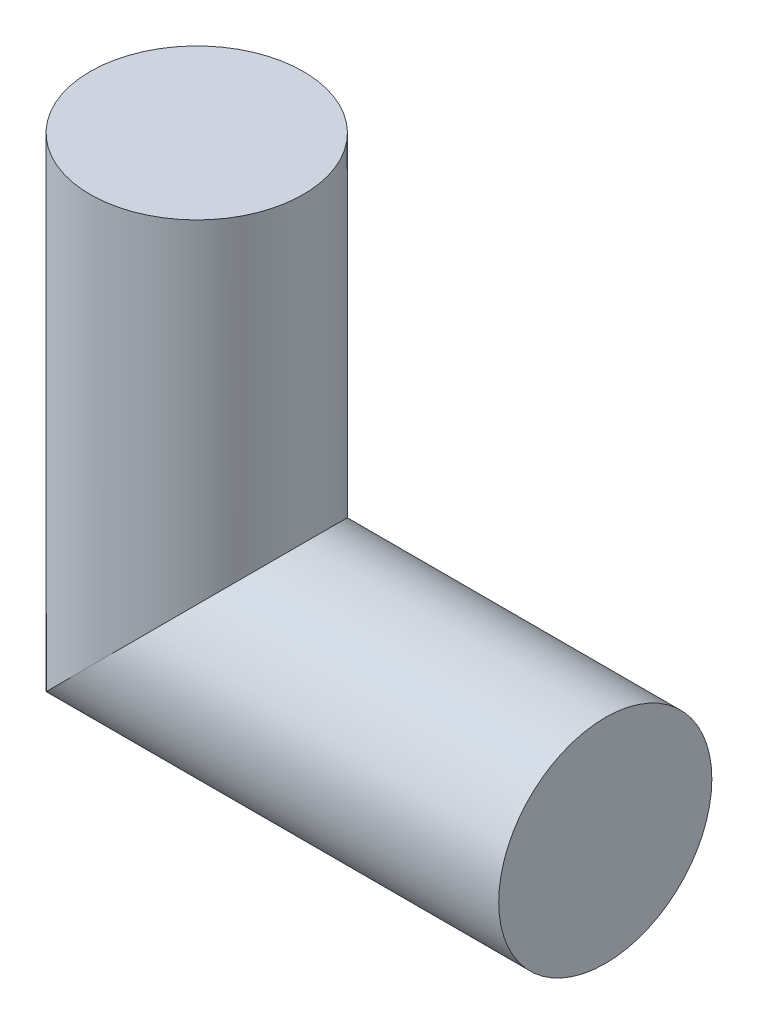
SolidWorks part; units mm, degrees
ref_plane "Front Plane" through (0, 0, 0) normal (0, 0, 1) x (1, 0, 0)
ref_plane "Top Plane" through (0, 0, 0) normal (0, 1, 0) x (1, 0, 0)
ref_plane "Right Plane" through (0, 0, 0) normal (1, 0, 0) x (0, 0, -1)
sketch "Sketch1" plane through (0, 0, 0) normal (1, 0, 0) x (0, 0, -1)
  circle A0 centre (0, 0) radius 6
  dimension "D1" = 12
sketch "Sketch2" plane through (0, 0, 0) normal (0, 0, 1) x (1, 0, 0)
  line L0 (0, 0) -> (-23, 0)
  line L1 (-23, 0) -> (-23, 23)
  dimension "D1" = 23
  dimension "D2" = 23
sweep "Sweep1" add profiles "Sketch1" path "Sketch2"
